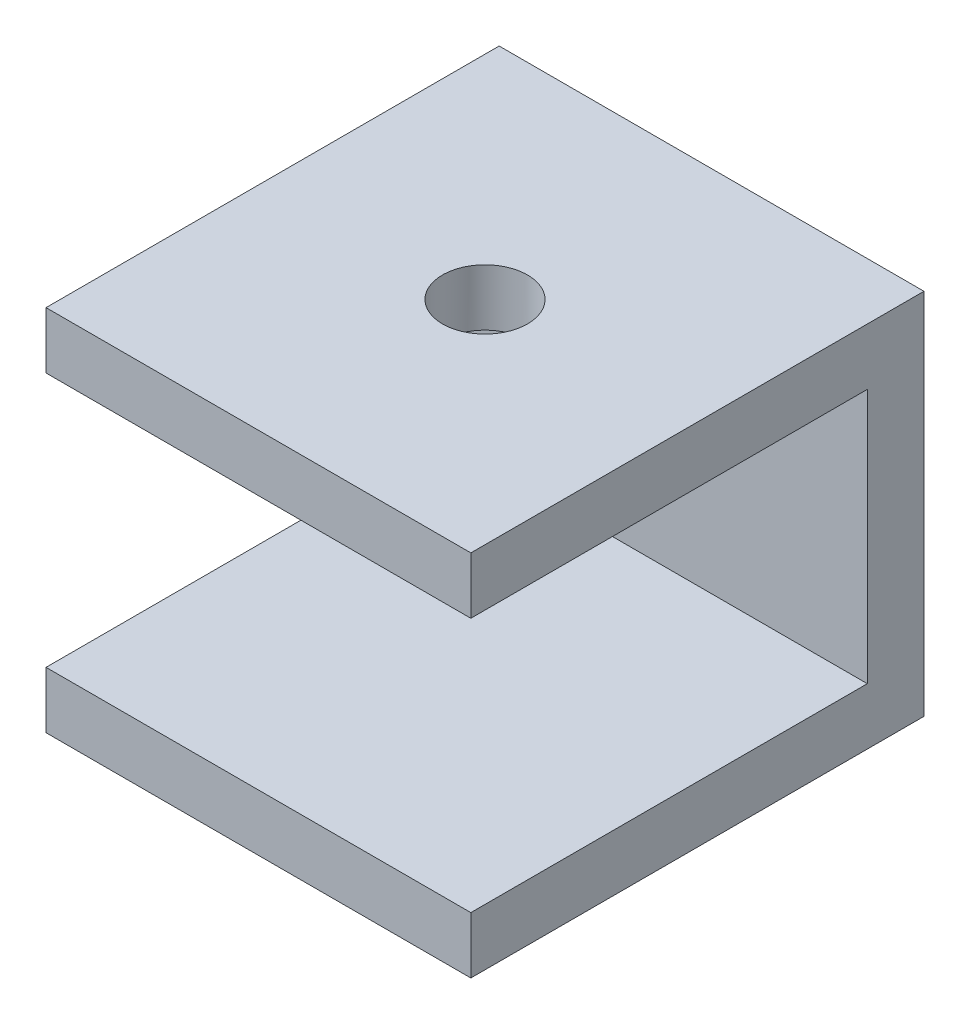
SolidWorks part; units mm, degrees
ref_plane "Front Plane" through (0, 0, 0) normal (0, 0, 1) x (1, 0, 0)
ref_plane "Top Plane" through (0, 0, 0) normal (0, 1, 0) x (1, 0, 0)
ref_plane "Right Plane" through (0, 0, 0) normal (1, 0, 0) x (0, 0, -1)
sketch "Sketch1" plane through (0, 0, 0) normal (1, 0, 0) x (0, 0, -1)
  line L0 (0, 0) -> (0, -13)
  line L1 (0, -13) -> (-16, -13)
  line L2 (-16, -13) -> (-16, -11)
  line L3 (-16, -11) -> (-2, -11)
  line L4 (-2, -11) -> (-2, -2)
  line L5 (-2, -2) -> (-16, -2)
  line L6 (-16, -2) -> (-16, 0)
  line L7 (-16, 0) -> (0, 0)
  dimension "D1" = 2
  dimension "D2" = 16
  dimension "D3" = 14
  dimension "D4" = 2
  dimension "D5" = 2
  dimension "D6" = 16
  dimension "D7" = 14
  dimension "D8" = 13
  dimension "D9" = 9
extrude "Boss-Extrude1" add sketch "Sketch1" against normal blind 15
sketch "Sketch2" plane through (0, 0, 0) normal (0, 1, 0) x (1, 0, 0)
  line L0 (-15, 0) -> (-15, -16) construction
  line L1 (-15, 0) -> (0, 0) construction
  circle A0 centre (-7.5, -8) radius 1.5
  dimension "D3" = 3
  dimension "D1" = 7.5
  dimension "D2" = 8
extrude "Cut-Extrude1" cut sketch "Sketch2" against normal up to next
